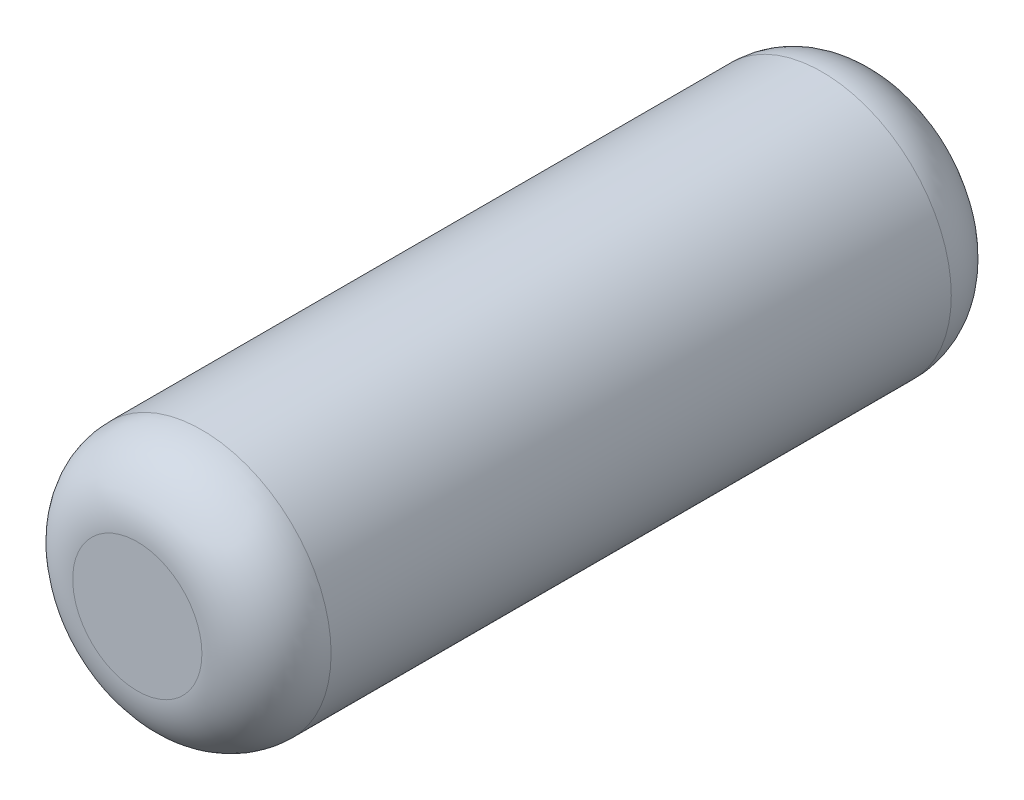
SolidWorks part; units mm, degrees
ref_plane "Alzado" through (0, 0, 0) normal (0, 0, 1) x (1, 0, 0)
ref_plane "Planta" through (0, 0, 0) normal (0, 1, 0) x (1, 0, 0)
ref_plane "Vista lateral" through (0, 0, 0) normal (1, 0, 0) x (0, 0, -1)
sketch "Croquis2" plane through (0, 0, 0) normal (0, 0, 1) x (1, 0, 0)
  circle A1 centre (0, 0) radius 5
  point P3 (0.255, -9.2609)
extrude "Saliente-Extruir1" add sketch "Croquis2" along normal blind 29
fillet "Redondeo3" radius 2.5 2 edges at (5, 0, 29) (5, 0, 0)
